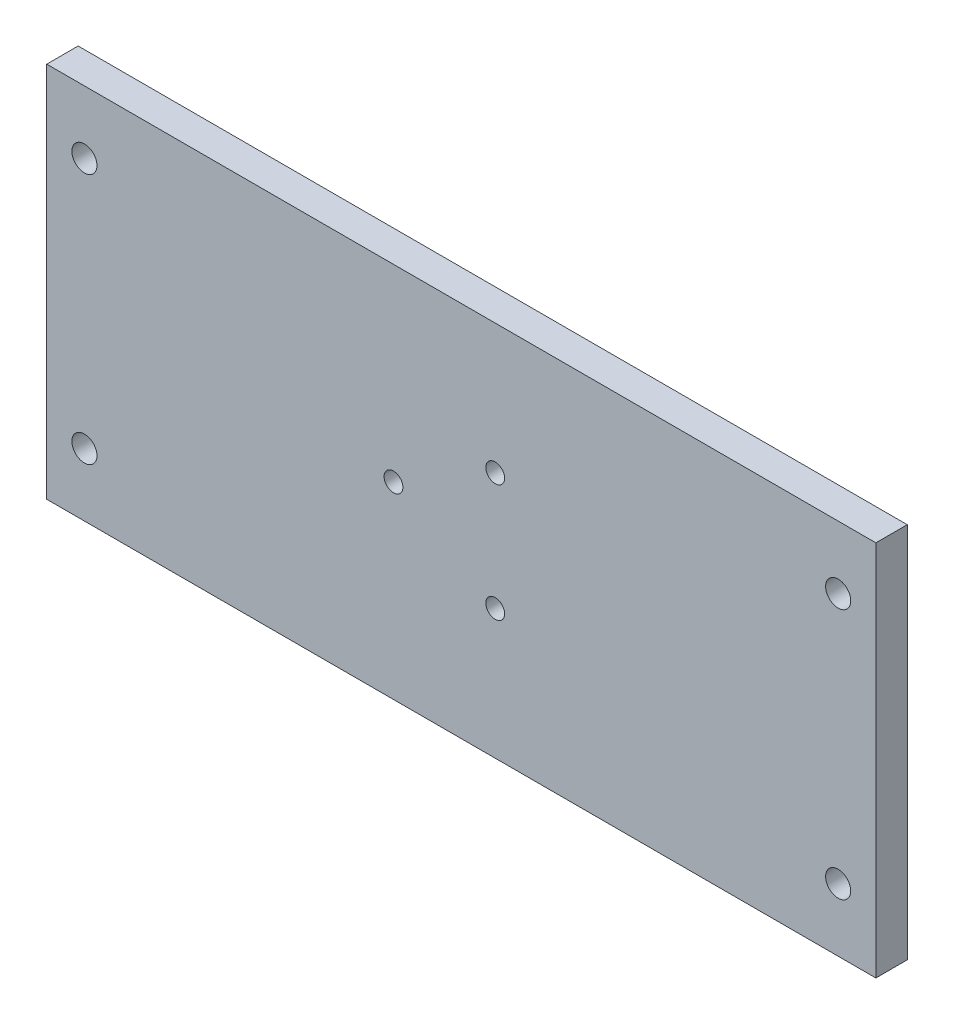
SolidWorks part; units mm, degrees
material "7075-T6 (SN)"
ref_plane "Front Plane" through (0, 0, 0) normal (0, 0, 1) x (1, 0, 0)
ref_plane "Top Plane" through (0, 0, 0) normal (0, 1, 0) x (1, 0, 0)
ref_plane "Right Plane" through (0, 0, 0) normal (1, 0, 0) x (0, 0, -1)
sketch "Sketch1" plane through (0, 0, 0) normal (0, 0, 1) x (1, 0, 0)
  line L1 (-70, -30) -> (70, -30)
  line L2 (-70, -30) -> (-70, 30)
  line L3 (-70, 30) -> (70, 30)
  line L4 (70, -30) -> (70, 30)
  line L5 (-70, -30) -> (70, 30) construction
  line L6 (-70, 30) -> (70, -30) construction
  point P0 (0, 0)
  dimension "D1" = 60
  dimension "D2" = 140
extrude "Boss-Extrude1" add sketch "Sketch1" along normal blind 5
sketch "Sketch2" plane through (0, 0, 5) normal (0, 0, 1) x (1, 0, 0)
  line L0 (-70, 30) -> (-70, -30) construction
  line L1 (-60, -20) -> (60, -20) construction
  line L2 (-60, -20) -> (-60, 20) construction
  line L3 (-60, 20) -> (60, 20) construction
  line L4 (60, -20) -> (60, 20) construction
  line L5 (-60, -20) -> (60, 20) construction
  line L6 (-60, 20) -> (60, -20) construction
  line L7 (70, 30) -> (-70, 30) construction
  circle A0 centre (-60, 20) radius 2
  circle A1 centre (60, 20) radius 2
  circle A2 centre (60, -20) radius 2
  circle A3 centre (-60, -20) radius 2
  point P0 (0, 0)
  dimension "D3" = 4
  dimension "D4" = 4
  dimension "D5" = 4
  dimension "D6" = 4
  dimension "D1" = 10
  dimension "D2" = 10
extrude "Cut-Extrude1" cut sketch "Sketch2" against normal up to next
sketch "Sketch3" plane through (0, 0, 5) normal (0, 0, 1) x (1, 0, 0)
  line L0 (-70, -30) -> (70, -30) construction
  line L1 (-70, 30) -> (-66, 30)
  line L2 (-70, 30) -> (-70, -30)
  line L3 (-70, -30) -> (-66, -30)
  line L4 (-66, 30) -> (-66, -30)
  line L6 (70, 30) -> (66, 30)
  line L7 (70, 30) -> (70, -30)
  line L8 (70, -30) -> (66, -30)
  line L9 (66, 30) -> (66, -30)
  dimension "D1" = 4
  dimension "D2" = 4
extrude "Cut-Extrude2" cut sketch "Sketch3" against normal through all
sketch "Sketch4" plane through (0, 0, 5) normal (0, 0, 1) x (1, 0, 0)
  line L0 (0, 0) -> (-14.5633, 0) construction
  line L1 (0, 0) -> (7.7051, 13.3456) construction
  line L2 (0, 0) -> (7.9457, -13.7624) construction
  circle A0 centre (0, 0) radius 10.795 construction
  circle A1 centre (5.3975, 9.3487) radius 1.5
  circle A2 centre (5.3975, -9.3487) radius 1.5
  circle A3 centre (-10.795, 0) radius 1.5
  dimension "D3" = 21.59
  dimension "D4" = 3
  dimension "D5" = 3
  dimension "D6" = 3
  dimension "D1" = 120
  dimension "D2" = 120
extrude "Cut-Extrude3" cut sketch "Sketch4" against normal up to next
